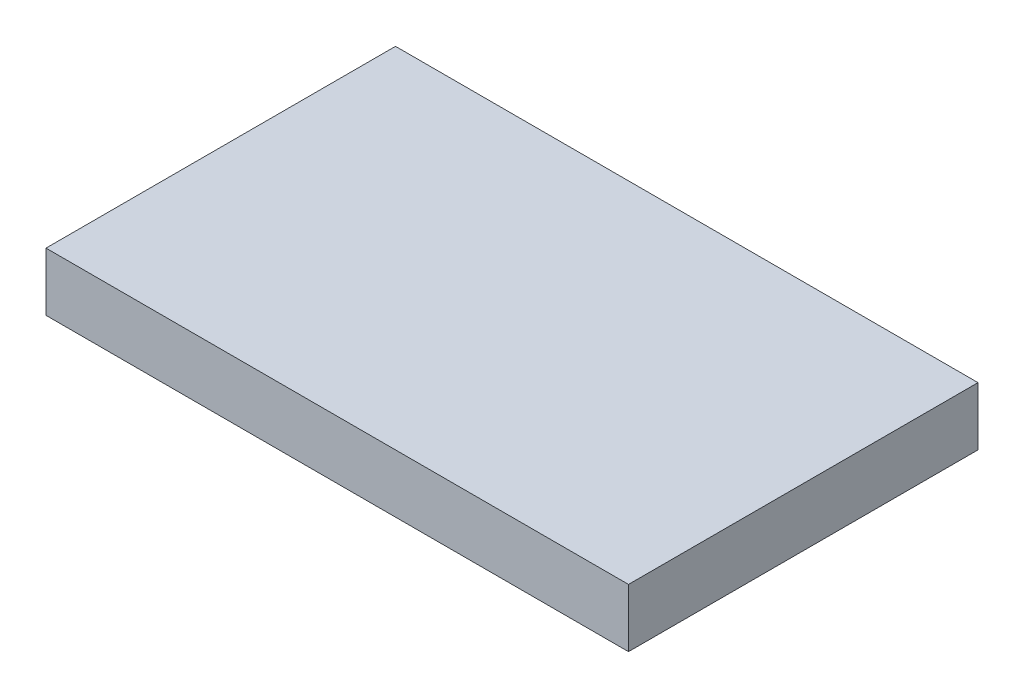
SolidWorks part; units mm, degrees
material "Maple"
ref_plane "Front Plane" through (0, 0, 0) normal (0, 0, 1) x (1, 0, 0)
ref_plane "Top Plane" through (0, 0, 0) normal (0, 1, 0) x (1, 0, 0)
ref_plane "Right Plane" through (0, 0, 0) normal (1, 0, 0) x (0, 0, -1)
sketch "Sketch1" plane through (0, 0, 0) normal (0, 1, 0) x (1, 0, 0)
  line L0 (0, 0) -> (127, 0)
  line L1 (0, 0) -> (0, 76.2)
  line L2 (127, 0) -> (127, 76.2)
  line L3 (0, 76.2) -> (127, 76.2)
  dimension "D1" = 127
  dimension "D2" = 76.2
extrude "Boss-Extrude1" add sketch "Sketch1" along normal blind 12.7
